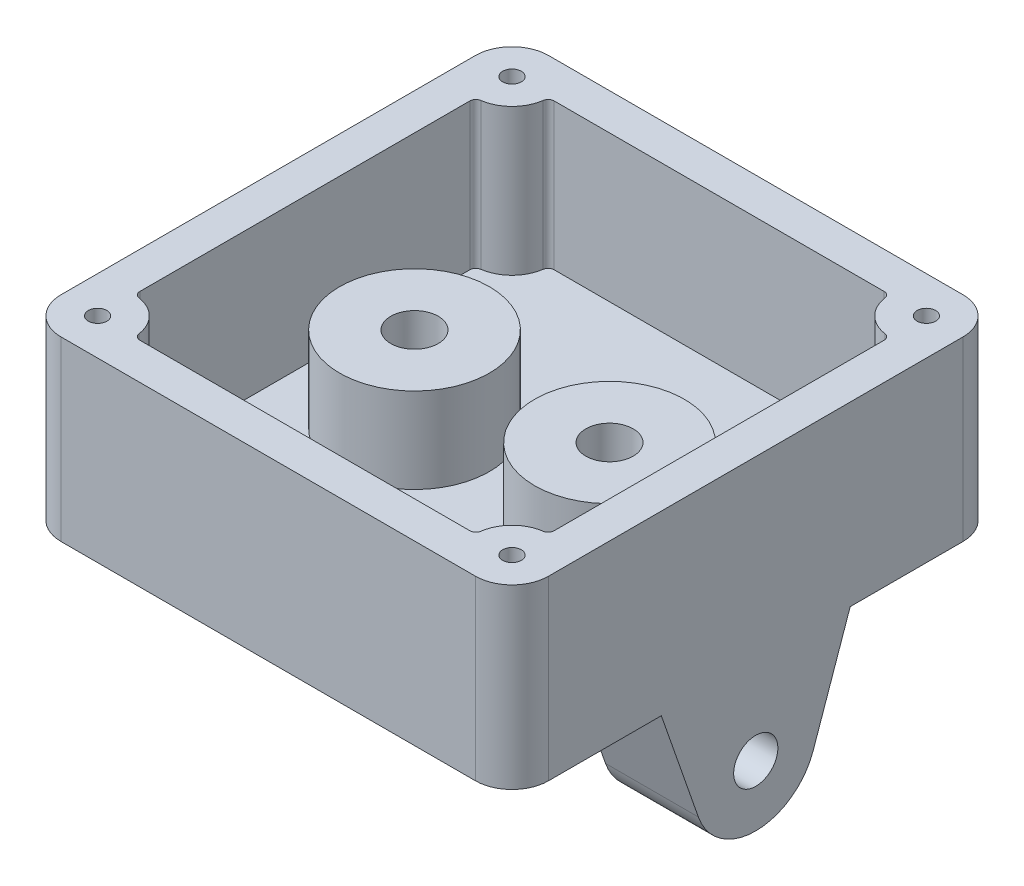
SolidWorks part; units mm, degrees
ref_plane "Front Plane" through (0, 0, 0) normal (0, 0, 1) x (1, 0, 0)
ref_plane "Top Plane" through (0, 0, 0) normal (0, 1, 0) x (1, 0, 0)
ref_plane "Right Plane" through (0, 0, 0) normal (1, 0, 0) x (0, 0, -1)
sketch "Sketch1" plane through (0, 0, 0) normal (0, 1, 0) x (1, 0, 0)
  line L1 (-20, 20) -> (20, 20)
  line L2 (-20, 20) -> (-20, -20)
  line L3 (-20, -20) -> (20, -20)
  line L4 (20, 20) -> (20, -20)
  line L5 (-20, 20) -> (20, -20) construction
  line L6 (-20, -20) -> (20, 20) construction
  point P0 (0, 0)
  dimension "D1" = 40
  dimension "D2" = 40
extrude "Boss-Extrude1" add sketch "Sketch1" along normal blind 2.54
sketch "Sketch2" plane through (0, 2.54, 0) normal (0, 1, 0) x (1, 0, 0)
  line L26 (-20, 20) -> (20, 20)
  line L44 (-20, 20) -> (-20, -20)
  line L45 (-20, -20) -> (20, -20)
  line L49 (20, 20) -> (20, -20)
  line L50 (-20, 20) -> (20, -20) construction
  line L51 (-20, -20) -> (20, 20) construction
  line L55 (-17, 13.5359) -> (-17, -13.5359)
  line L56 (-13.5359, -17) -> (13.5359, -17)
  line L57 (17, 13.5359) -> (17, -13.5359)
  line L58 (-13.5359, 17) -> (13.5359, 17)
  line L63 (-17, 17) -> (-17, -17) construction
  line L64 (-17, -17) -> (17, -17) construction
  line L65 (17, 17) -> (17, -17) construction
  line L66 (-17, 17) -> (17, 17) construction
  line L68 (-14.8787, 14.8787) -> (14.8787, 14.8787) construction
  line L69 (-14.8787, 14.8787) -> (-14.8787, -14.8787) construction
  line L70 (-14.8787, -14.8787) -> (14.8787, -14.8787) construction
  line L71 (14.8787, 14.8787) -> (14.8787, -14.8787) construction
  line L72 (-14.8787, 14.8787) -> (14.8787, -14.8787) construction
  line L73 (-14.8787, -14.8787) -> (14.8787, 14.8787) construction
  arc A0 (-16.5714, -14.0308) -> (-14.0308, -16.5714) centre (-17, -17) cw
  arc A2 (14.0308, -16.5714) -> (16.5714, -14.0308) centre (17, -17) cw
  arc A4 (16.5714, 14.0308) -> (14.0308, 16.5714) centre (17, 17) cw
  arc A6 (-14.0308, 16.5714) -> (-16.5714, 14.0308) centre (-17, 17) cw
  arc A8 (-16.5714, -14.0308) -> (-17, -13.5359) centre (-16.5, -13.5359) cw
  arc A9 (-14.0308, -16.5714) -> (-13.5359, -17) centre (-13.5359, -16.5) ccw
  arc A10 (14.0308, -16.5714) -> (13.5359, -17) centre (13.5359, -16.5) cw
  arc A11 (16.5714, -14.0308) -> (17, -13.5359) centre (16.5, -13.5359) ccw
  arc A12 (16.5714, 14.0308) -> (17, 13.5359) centre (16.5, 13.5359) cw
  arc A13 (14.0308, 16.5714) -> (13.5359, 17) centre (13.5359, 16.5) ccw
  arc A14 (-14.0308, 16.5714) -> (-13.5359, 17) centre (-13.5359, 16.5) cw
  arc A15 (-16.5714, 14.0308) -> (-17, 13.5359) centre (-16.5, 13.5359) ccw
  point P0 (0, 0)
  point P21 (0, 0)
  point P44 (0, 0)
  dimension "D2" = 3
  dimension "D3" = 0.5
  dimension "D1" = 3
  dimension "D4" = 29.7574
extrude "Boss-Extrude2" add sketch "Sketch2" along normal blind 12
sketch "Sketch4" plane through (-20, 0, 0) normal (-1, 0, 0) x (0, 0, 1)
  line L0 (7.7485, 0) -> (4.709, -8.7193)
  line L1 (-20, 0) -> (20, 0) construction
  line L2 (-4.709, -8.7193) -> (-7.7485, 0)
  line L3 (7.7485, 0) -> (-7.7485, 0)
  arc A0 (4.709, -8.7193) -> (-4.709, -8.7193) centre (0, -7.0778) cw
  circle A1 centre (0, -7.0778) radius 1.8138
extrude "Boss-Extrude4" add sketch "Sketch4" against normal blind 7.62
mirror "Mirror1" about plane through (0, 0, 0) normal (1, 0, 0) of "Boss-Extrude4"
sketch "Sketch9" plane through (0, 2.54, 0) normal (0, 1, 0) x (1, 0, 0)
  line L0 (0, -1.397) -> (0, 1.397) construction
  circle A0 centre (8, 0) radius 1.945
  circle A1 centre (8, 0) radius 6.145
  circle A2 centre (-8, 0) radius 6.145
  circle A3 centre (-8, 0) radius 1.945
  dimension "D1" = 3.89
  dimension "D2" = 4.2
  dimension "D3" = 8
extrude "Boss-Extrude5" add sketch "Sketch9" along normal blind 7
fillet "Fillet1" radius 3 4 edges at (20, 7.27, 20) (-20, 7.27, 20) (-20, 7.27, -20) (20, 7.27, -20)
sketch "Sketch10" plane through (0, 14.54, 0) normal (0, 1, 0) x (1, 0, 0)
  circle A0 centre (-17, 17) radius 0.7617
  circle A1 centre (17, 17) radius 0.7617
  circle A2 centre (-17, -17) radius 0.7617
  circle A3 centre (17, -17) radius 0.7617
  dimension "D1" = 1.5234
extrude "Cut-Extrude1" cut sketch "Sketch10" against normal blind 8
